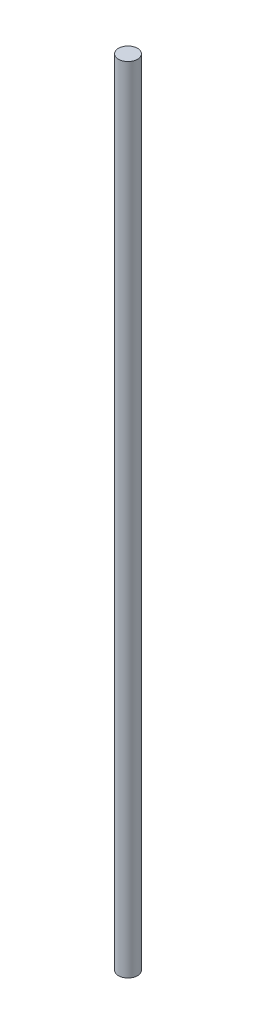
SolidWorks part; units mm, degrees
ref_plane "Front Plane" through (0, 0, 0) normal (0, 0, 1) x (1, 0, 0)
ref_plane "Top Plane" through (0, 0, 0) normal (0, 1, 0) x (1, 0, 0)
ref_plane "Right Plane" through (0, 0, 0) normal (1, 0, 0) x (0, 0, -1)
sketch "Sketch1" plane through (0, 0, 0) normal (0, 1, 0) x (1, 0, 0)
  circle A0 centre (0, 0) radius 3
  dimension "D1" = 6
extrude "Boss-Extrude1" add sketch "Sketch1" along normal blind 250
